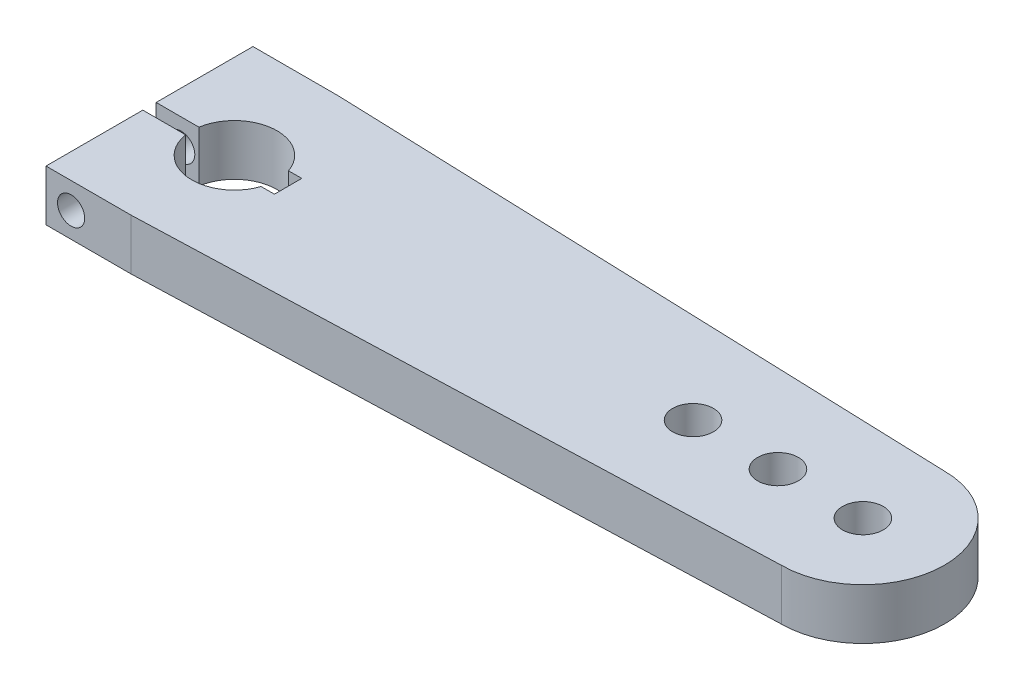
SolidWorks part; units mm, degrees
ref_plane "Front Plane" through (0, 0, 0) normal (0, 0, 1) x (1, 0, 0)
ref_plane "Top Plane" through (0, 0, 0) normal (0, 1, 0) x (1, 0, 0)
ref_plane "Right Plane" through (0, 0, 0) normal (1, 0, 0) x (0, 0, -1)
sketch "Sketch1" plane through (0, 0, 0) normal (0, 1, 0) x (1, 0, 0)
  line L0 (-77.0425, -2.7737) -> (-58.854, -2.7737) construction
  line L1 (-92.8425, 27.6867) -> (92.1575, 21.2263)
  line L2 (-117.8425, 27.6867) -> (-117.8425, -33.234)
  line L3 (-92.8425, -33.234) -> (92.1575, -26.7737)
  line L4 (-92.8425, -33.234) -> (-117.8425, -33.234)
  line L5 (-80.9555, 1.2513) -> (-77.0425, 1.2513)
  line L6 (-92.8425, 27.6867) -> (-117.8425, 27.6867)
  line L7 (-80.9555, -6.7987) -> (-77.0425, -6.7987)
  line L8 (-77.0425, 1.2513) -> (-77.0425, -6.7987)
  arc A0 (-80.9555, 1.2513) -> (-80.9555, -6.7987) centre (-92.8425, -2.7737) ccw
  circle A1 centre (67.1575, -2.7737) radius 6
  circle A2 centre (42.1575, -2.7737) radius 6
  circle A3 centre (92.1575, -2.7737) radius 6
  arc A4 (92.1575, 21.2263) -> (92.1575, -26.7737) centre (92.1575, -2.7737) cw
  dimension "D1" = 160
  dimension "D3" = 12
  dimension "D4" = 12
  dimension "D5" = 12
  dimension "D7" = 25.1
  dimension "D10" = 24
  dimension "D2" = 25
  dimension "D6" = 25
  dimension "D8" = 8.05
  dimension "D9" = 15.8
  dimension "D11" = 210
  dimension "D12" = 88
  dimension "D13" = 88
  dimension "D14" = 60.9207
extrude "Boss-Extrude1" add sketch "Sketch1" along normal blind 15
sketch "Sketch2" plane through (0.4264, 0, 0) normal (0, 0, -1) x (-1, 0, 0)
  circle A0 centre (110.8886, 7.3693) radius 4
  dimension "D1" = 8
extrude "Cut-Extrude1" cut sketch "Sketch2" against normal through all both and the other way through all
sketch "Sketch3" plane through (0, 15, 0) normal (0, 1, 0) x (1, 0, 0)
  line L1 (-124.0135, -0.8133) -> (-98.568, -0.8133)
  line L2 (-124.0135, -0.8133) -> (-124.0135, -4.734)
  line L3 (-124.0135, -4.734) -> (-98.568, -4.734)
  line L4 (-98.568, -0.8133) -> (-98.568, -4.734)
  line L6 (-92.8425, 27.6867) -> (-117.8425, 27.6867) construction
  dimension "D1" = 28.5
  dimension "D2" = 28.5
extrude "Cut-Extrude2" cut sketch "Sketch3" against normal through all contours L1 L4 L3 L2
